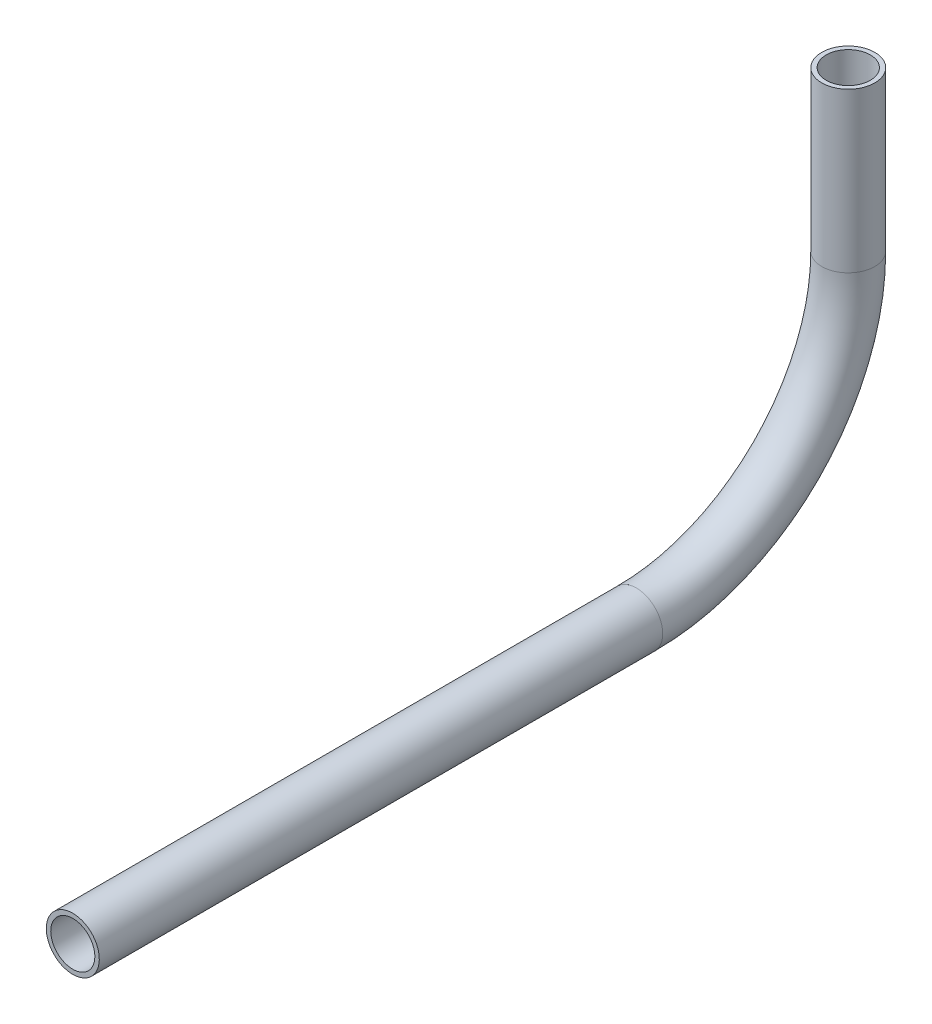
SolidWorks part; units mm, degrees
ref_plane "Front Plane" through (0, 0, 0) normal (0, 0, 1) x (1, 0, 0)
ref_plane "Top Plane" through (0, 0, 0) normal (0, 1, 0) x (1, 0, 0)
ref_plane "Right Plane" through (0, 0, 0) normal (1, 0, 0) x (0, 0, -1)
sketch "Sketch1" plane through (0, 0, 0) normal (1, 0, 0) x (0, 0, -1)
  line L0 (-303.1646, 670.1656) -> (-168.1736, 670.1656)
  line L1 (-117.3736, 720.9656) -> (-117.3736, 759.0656)
  arc A0 (-168.1736, 670.1656) -> (-117.3736, 720.9656) centre (-168.1736, 720.9656) ccw
  dimension "D1" = 50.8
  dimension "D2" = 38.1
other "Pipe 0.5 SCH 40(1)"
ref_plane "Plane1" through (0, 670.1656, 303.1646) normal (0, 0, -1) x (0, 1, 0)
sketch "Sketch11" plane through (0, 670.1656, 303.1646) normal (0, 0, -1) x (0, 1, 0)
  circle A0 centre (0, 0) radius 5.2832
  circle A1 centre (0, 0) radius 6.35
  point P5 (0, 0)
  dimension "In_dia" = 10.5664
  dimension "Out_dia" = 12.7
